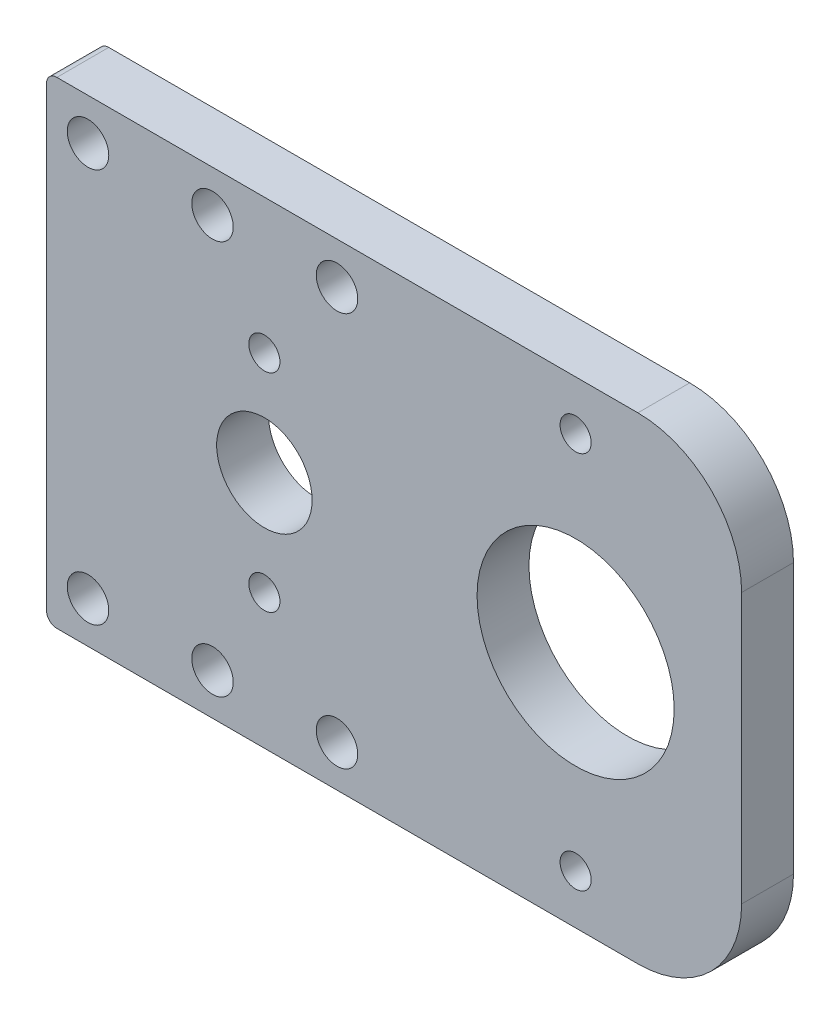
SolidWorks part; units mm, degrees
material "Acrylic (Medium-high impact)"
ref_plane "Front Plane" through (0, 0, 0) normal (0, 0, 1) x (1, 0, 0)
ref_plane "Top Plane" through (0, 0, 0) normal (0, 1, 0) x (1, 0, 0)
ref_plane "Right Plane" through (0, 0, 0) normal (1, 0, 0) x (0, 0, -1)
sketch "Sketch1" plane through (0, 0, 0) normal (0, 0, 1) x (1, 0, 0)
  line L0 (-25.3491, 0) -> (24.7222, 0) construction
  line L1 (40, -23) -> (-40, -23)
  line L2 (40, -23) -> (40, 23)
  line L3 (40, 23) -> (-40, 23)
  line L4 (-40, -23) -> (-40, 23)
  line L5 (40, -23) -> (-40, 23) construction
  line L6 (40, 23) -> (-40, -23) construction
  line L7 (30, 0) -> (30, 18.25)
  line L8 (-40, 23) -> (-25, 23)
  line L9 (-25, 23) -> (-25, -23)
  line L10 (0, 0) -> (0, -10)
  circle A0 centre (0, 0) radius 4.6
  circle A1 centre (30, 0) radius 9.5
  circle A2 centre (30, 18.25) radius 1.5
  circle A3 centre (30, -18.25) radius 1.5
  circle A4 centre (0, -10) radius 1.5
  circle A5 centre (0, 10) radius 1.5
  point P0 (0, 0)
  dimension "D1" = 9.2
  dimension "D2" = 19
  dimension "D7" = 3
  dimension "D10" = 3
  dimension "D3" = 46
  dimension "D4" = 30
  dimension "D5" = 80
  dimension "D6" = 18.25
  dimension "D8" = 15
  dimension "D9" = 10
extrude "Boss-Extrude1" add sketch "Sketch1" along normal blind 5
sketch "Sketch2" plane through (0, 0, 5) normal (0, 0, 1) x (1, 0, 0)
  line L0 (-25, -23) -> (-25, 23)
  line L1 (-25, -23) -> (-5, -23)
  line L2 (-25, 23) -> (-5, 23)
  line L3 (-5, -23) -> (-5, 23)
  line L4 (-25, 23) -> (-25, -23)
  line L5 (-25, -23) -> (40, -23)
  line L6 (40, -23) -> (40, 23)
  line L7 (40, 23) -> (-25, 23)
  line L9 (-25, -23) -> (40, -23)
  line L10 (40, -23) -> (40, 23)
  line L11 (40, 23) -> (-25, 23)
  line L12 (-17, 19) -> (-25, 19)
  line L13 (-17, 19) -> (-5, 19)
  line L14 (-5, 19) -> (7, 19)
  line L16 (-5, 0) -> (-25, 0)
  line L20 (-25, 23) -> (-25, -23)
  circle A0 centre (-17, 19) radius 2
  circle A1 centre (-5, 19) radius 2
  circle A5 centre (7, 19) radius 2
  circle A6 centre (7, -19) radius 2
  circle A7 centre (-5, -19) radius 2
  circle A8 centre (-17, -19) radius 2
  dimension "D5" = 4
  dimension "D6" = 4
  dimension "D7" = 19
  dimension "D8" = 4
  dimension "D2" = 20
  dimension "D3" = 12
  dimension "D4" = 12
  dimension "D9" = 8
  dimension "D1" = 0
extrude "Cut-Extrude1" cut sketch "Sketch2" against normal blind 10
sketch "Sketch3" plane through (0, 0, 5) normal (0, 0, 1) x (1, 0, 0)
  line L0 (-25, 23) -> (-21, 23)
  line L1 (-21, 23) -> (-21, -23)
  line L4 (40, 23) -> (-25, 23)
  line L5 (-25, 23) -> (-25, -23)
  line L6 (-25, -23) -> (40, -23)
  line L7 (40, -23) -> (40, 23)
  line L8 (40, 23) -> (-25, 23)
  line L9 (-25, 23) -> (-25, -23)
  line L10 (-25, -23) -> (40, -23)
  line L11 (40, -23) -> (40, 23)
  line M10 (40, 23) -> (-25, 23)
  line M11 (-25, 23) -> (-25, -23)
  line M12 (-25, -23) -> (40, -23)
  dimension "D2" = 4
  dimension "D1" = 0
extrude "Cut-Extrude2" cut sketch "Sketch3" against normal through all contours L1 M10 M11 M12
sketch "Sketch4" plane through (0, 0, 5) normal (0, 0, 1) x (1, 0, 0)
  line L1 (40, 23) -> (46, 23)
  line L2 (40, 23) -> (40, -23)
  line L3 (40, -23) -> (46, -23)
  line L4 (40, 23) -> (-21, 23)
  line L5 (-21, 23) -> (-21, -23)
  line L6 (-21, -23) -> (40, -23)
  line L7 (40, -23) -> (40, 23)
  line L8 (40, 23) -> (-21, 23)
  line L9 (-21, 23) -> (-21, -23)
  line L10 (-21, -23) -> (40, -23)
  line L11 (40, -23) -> (40, 23)
  line L12 (46, 23) -> (46, -23)
  line M19 (40, -23) -> (40, 23)
  dimension "D2" = 6
  dimension "D1" = 0
extrude "Boss-Extrude2" add sketch "Sketch4" against normal up to surface (5 mm away) contours L12 L1 L3 M19 up to face at (-15, 19, 0)
fillet "Fillet1" radius 10 2 edges at (46, 23, 2.5) (46, -23, 2.5)
fillet "Fillet2" radius 1 2 edges at (-21, 23, 2.5) (-21, -23, 2.5)
